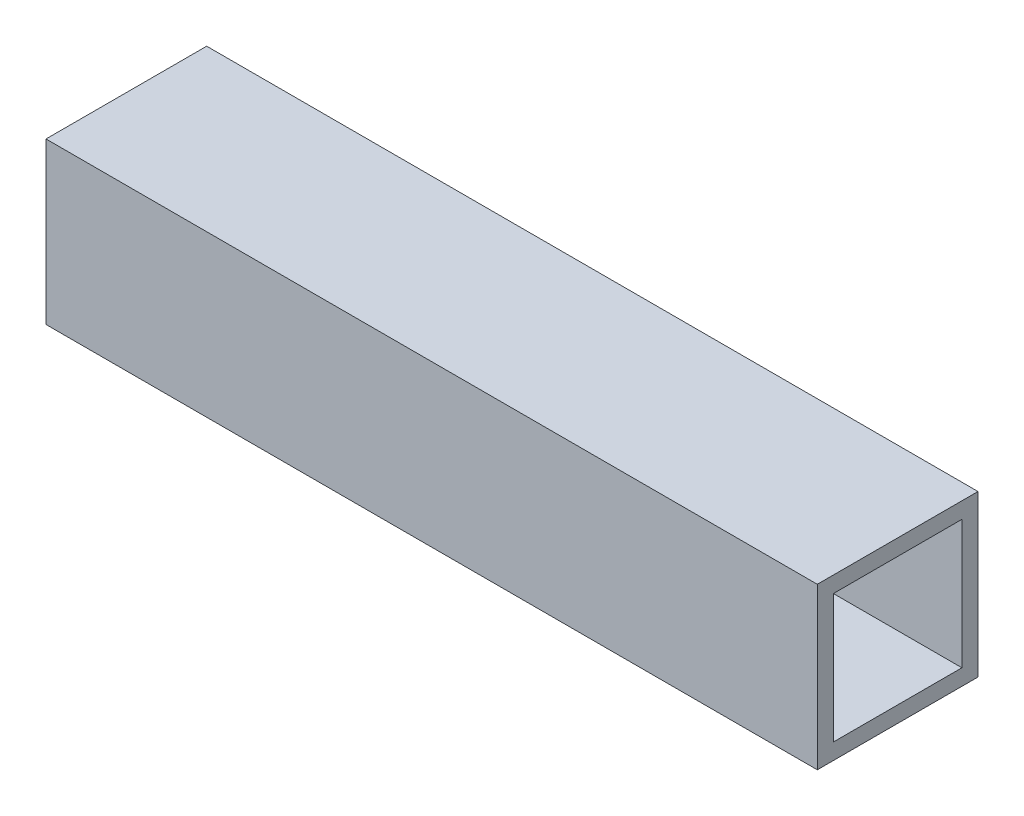
SolidWorks part; units mm, degrees
ref_plane "Front" through (0, 0, 0) normal (0, 0, 1) x (1, 0, 0)
ref_plane "Top" through (0, 0, 0) normal (0, 1, 0) x (1, 0, 0)
ref_plane "Right" through (0, 0, 0) normal (1, 0, 0) x (0, 0, -1)
sketch "Sketch1" plane through (0, 0, 0) normal (1, 0, 0) x (0, 0, -1)
  line L1 (-15.875, -15.875) -> (15.875, -15.875)
  line L2 (-15.875, -15.875) -> (-15.875, 15.875)
  line L3 (-15.875, 15.875) -> (15.875, 15.875)
  line L4 (15.875, -15.875) -> (15.875, 15.875)
  line L5 (-15.875, -15.875) -> (15.875, 15.875) construction
  line L6 (-15.875, 15.875) -> (15.875, -15.875) construction
  line L7 (-12.7, -12.7) -> (12.7, -12.7)
  line L8 (-12.7, -12.7) -> (-12.7, 12.7)
  line L9 (-12.7, 12.7) -> (12.7, 12.7)
  line L10 (12.7, -12.7) -> (12.7, 12.7)
  line L11 (-12.7, -12.7) -> (12.7, 12.7) construction
  line L12 (-12.7, 12.7) -> (12.7, -12.7) construction
  point P0 (0, 0)
  point P6 (0, 0)
  dimension "D1" = 31.75
  dimension "D2" = 31.75
  dimension "D3" = 3.175
  dimension "D4" = 3.175
extrude "Boss-Extrude1" add sketch "Sketch1" along normal mid plane 152.4
equation "\"Height\"=31.75"
equation "\"D1@Sketch1\"=\"Height\""
equation "\"D2@Sketch1\"=\"Height\""
equation "\"Thicknesss\"=3.175"
equation "\"D3@Sketch1\"=\"Thicknesss\""
equation "\"D4@Sketch1\"=\"Thicknesss\""
equation "\"Length\"=152.4"
equation "\"D1@Boss-Extrude1\"=\"Length\""
